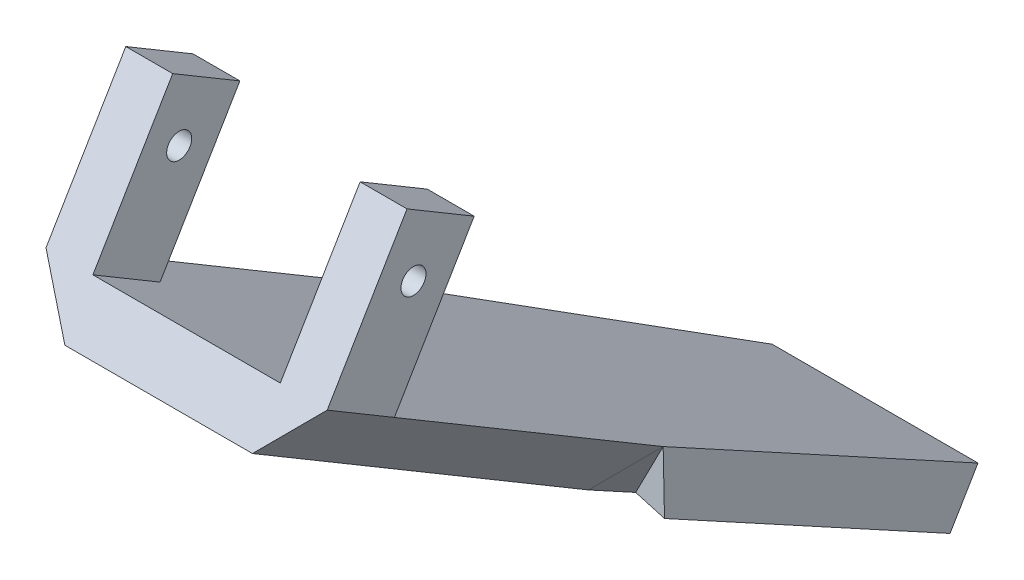
SolidWorks part; units mm, degrees
material "ABS PC"
ref_plane "Front Plane" through (0, 0, 0) normal (0, 0, 1) x (1, 0, 0)
ref_plane "Top Plane" through (0, 0, 0) normal (0, 1, 0) x (1, 0, 0)
ref_plane "Right Plane" through (0, 0, 0) normal (1, 0, 0) x (0, 0, -1)
sketch "Sketch2" plane through (0, 107.5652, -63.8831) normal (0, -0.8598, 0.5106) x (1, 0, 0)
  line L0 (-16.7267, 3.2269) -> (-22.8499, 69.8597)
  line L1 (-22.8499, 69.8597) -> (22.8499, 69.8597)
  line L2 (22.8499, 69.8597) -> (16.7267, 3.2269)
  line L3 (16.7267, 3.2269) -> (-16.7267, 3.2269)
extrude "Boss-Extrude1" add sketch "Sketch2" along normal blind 8.89
sketch "Sketch3" plane through (0, 99.9216, -59.3436) normal (0, -0.8598, 0.5106) x (1, 0, 0)
  line L0 (22.8499, 69.8597) -> (-22.8499, 69.8597) construction
  line L1 (-15.24, 69.8597) -> (15.24, 69.8597)
  line L2 (-15.24, 69.8597) -> (-15.24, 3.2269)
  line L3 (-15.24, 3.2269) -> (15.24, 3.2269)
  line L4 (15.24, 69.8597) -> (15.24, 3.2269)
  line L5 (-16.7267, 3.2269) -> (16.7267, 3.2269) construction
  dimension "D1" = 30.48
  dimension "D2" = 15.24
ref_plane "Plane1" through (52.0682, 40.7651, -18.6454) normal (-0.7578, -0.5933, 0.2714) x (0.37, -0.0482, 0.9278)
sketch "Sketch9" plane through (52.0682, 40.7651, -18.6454) normal (-0.7578, -0.5933, 0.2714) x (0.37, -0.0482, 0.9278)
  line L0 (-63.0204, 75.317) -> (-51.7431, 58.9374) construction
  line L1 (-18.9035, 126.3959) -> (19.1965, 126.3959)
  line L2 (-18.9035, 126.3959) -> (-18.9035, -44.0988)
  line L3 (-18.9035, -44.0988) -> (19.1965, -44.0988)
  line L4 (19.1965, 126.3959) -> (19.1965, -44.0988)
  dimension "D1" = 38.1
extrude "Cut-Extrude1" cut sketch "Sketch9" along normal blind 10.16
sketch "Sketch10" plane through (0, 99.9216, -59.3436) normal (0, -0.8598, 0.5106) x (1, 0, 0)
  line L0 (0, 69.8597) -> (0, 3.2269) construction
  line L1 (-15.24, 69.8597) -> (15.24, 69.8597) construction
  line L2 (-15.24, 3.2269) -> (15.24, 3.2269) construction
ref_plane "Plane4" through (0, 0, 0) normal (-1, 0, 0) x (0, 0, 1)
mirror "Mirror1" about plane through (0, 0, 0) normal (-1, 0, 0) of "Cut-Extrude1"
sketch "Sketch11" plane through (0, 35.6728, 60.0652) normal (0, 0.5106, 0.8598) x (1, 0, 0)
  line L0 (-22.8499, 125.1052) -> (-15.24, 116.2152)
  line L1 (-15.24, 116.2152) -> (15.24, 116.2152)
  line L2 (15.24, 116.2152) -> (22.8499, 125.1052)
  line L3 (22.8499, 125.1052) -> (-22.8499, 125.1052)
extrude "Boss-Extrude2" add sketch "Sketch11" along normal blind 63.5
sketch "Sketch12" plane through (0, 107.5652, -63.8831) normal (0, 0.8598, -0.5106) x (-1, 0, 0)
  line L1 (-22.8499, 133.3597) -> (-15.2299, 133.3597)
  line L2 (-22.8499, 133.3597) -> (-22.8499, 120.6597)
  line L3 (-22.8499, 120.6597) -> (-15.2299, 120.6597)
  line L4 (-15.2299, 133.3597) -> (-15.2299, 120.6597)
  dimension "D1" = 12.7
  dimension "D2" = 7.62
extrude "Boss-Extrude3" add sketch "Sketch12" along normal blind 25.4 contours L4 L3 L2 L1
ref_plane "Plane5" through (0, 0, 0) normal (1, 0, 0) x (0, 0, -1)
mirror "Mirror2" about plane through (0, 0, 0) normal (1, 0, 0) of "Boss-Extrude3"
sketch "Sketch13" plane through (-22.8499, 0, 0) normal (-1, 0, 0) x (0, 0, 1)
  line L0 (37.8092, 197.5022) -> (50.7793, 175.6633) construction
  line L2 (50.7793, 175.6633) -> (39.8599, 169.1782) construction
  circle A0 centre (36.7593, 186.8344) radius 2.032
  dimension "D1" = 4.064
  dimension "D2" = 6.35
  dimension "D3" = 16.764
extrude "Cut-Extrude2" cut sketch "Sketch13" against normal through all
